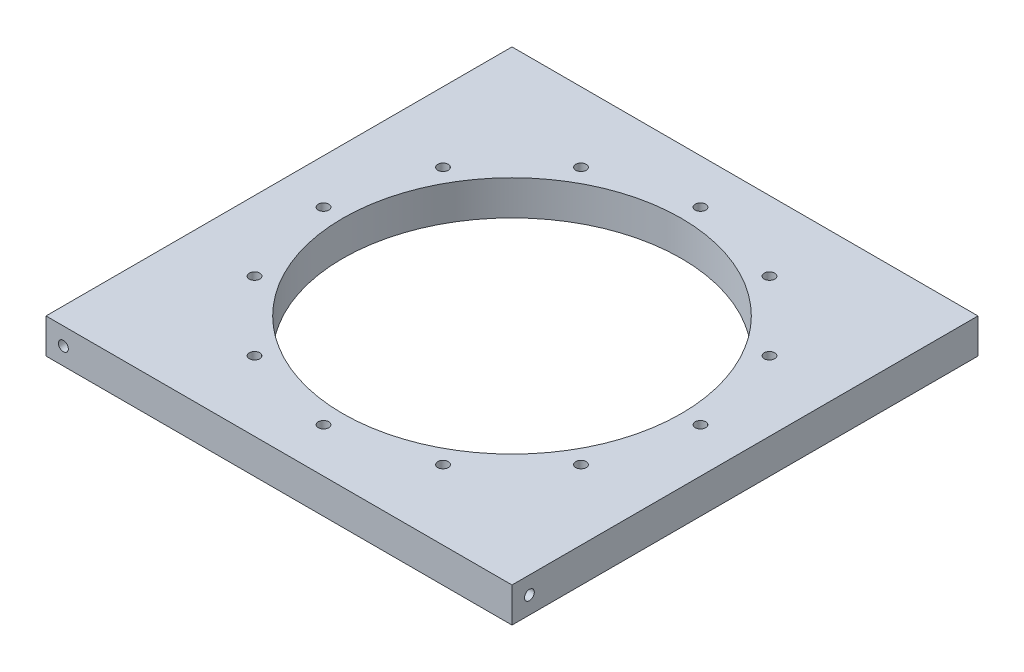
SolidWorks part; units mm, degrees
material "6061-T6 (SS)"
ref_plane "Front Plane" through (0, 0, 0) normal (0, 0, 1) x (1, 0, 0)
ref_plane "Top Plane" through (0, 0, 0) normal (0, 1, 0) x (1, 0, 0)
ref_plane "Right Plane" through (0, 0, 0) normal (1, 0, 0) x (0, 0, -1)
sketch "Sketch1" plane through (0, 0, 0) normal (0, 1, 0) x (1, 0, 0)
  line L5 (0, 0) -> (127.635, 0)
  line L6 (0, 0) -> (0, 127.635)
  line L7 (0, 127.635) -> (127.635, 127.635)
  line L8 (127.635, 0) -> (127.635, 127.635)
  dimension "D1" = 127.635
  dimension "D2" = 127.635
extrude "Boss-Extrude1" add sketch "Sketch1" along normal blind 9.525 contours L5 L8 L7 L6
sketch "Sketch5" plane through (0, 9.525, 0) normal (0, 1, 0) x (1, 0, 0)
  line L0 (63.8175, 0) -> (63.8175, 127.635) construction
  line L3 (0, 0) -> (127.635, 0) construction
  line L8 (0, 127.635) -> (127.635, 127.635) construction
  circle A0 centre (63.8175, 63.8175) radius 46.355
  dimension "D1" = 92.71
extrude "Cut-Extrude1" cut sketch "Sketch5" against normal blind 9.525 contours L0 A0 | A0 L0
sketch "Sketch11" plane through (0, 9.525, 0) normal (0, 1, 0) x (1, 0, 0)
  line L0 (63.8175, 63.8175) -> (63.8175, 115.443) construction
  circle A0 centre (63.8175, 115.443) radius 1.4351
  dimension "D2" = 2.8702
  dimension "D1" = 51.6255
extrude "Cut-Extrude3" cut sketch "Sketch11" against normal through all contours A0
pattern_circular "CirPattern1" count 12 over 360 about axis through (63.8175, 0, -63.8175) along (0, 1, 0) of "Cut-Extrude3"
sketch "Sketch6" plane through (127.635, 0, 0) normal (1, 0, 0) x (0, 0, -1)
  circle A0 centre (4.7625, 4.7625) radius 1.3526
  dimension "D1" = 2.7051
extrude "6-32 hole1" cut sketch "Sketch6" against normal blind 12.7
sketch "Sketch7" plane through (0, 0, -127.635) normal (0, 0, -1) x (-1, 0, 0)
  circle A0 centre (-122.8725, 4.7625) radius 1.3525
  dimension "D1" = 2.7051
sketch "Sketch8" plane through (0, 0, 0) normal (-1, 0, 0) x (0, 0, 1)
  circle A0 centre (-122.8725, 4.7625) radius 1.3525
  dimension "D1" = 2.7051
sketch "Sketch9" plane through (0, 0, 0) normal (0, 0, 1) x (1, 0, 0)
  circle A0 centre (4.7625, 4.7625) radius 1.3526
  dimension "D1" = 2.7051
extrude "6-32 hole2" cut sketch "Sketch7" against normal blind 12.7
extrude "6-32 hole3" cut sketch "Sketch8" against normal blind 12.7
extrude "6-32 hole4" cut sketch "Sketch9" against normal blind 12.7
